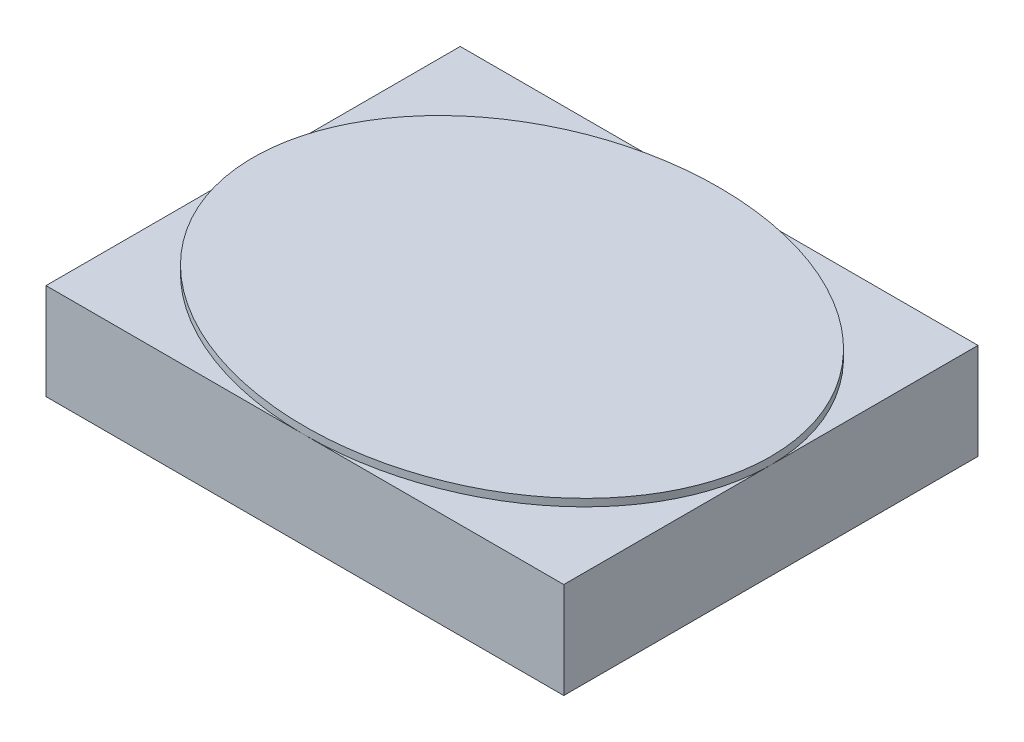
SolidWorks part; units mm, degrees
ref_plane "Front Plane" through (0, 0, 0) normal (0, 0, 1) x (1, 0, 0)
ref_plane "Top Plane" through (0, 0, 0) normal (0, 1, 0) x (1, 0, 0)
ref_plane "Right Plane" through (0, 0, 0) normal (1, 0, 0) x (0, 0, -1)
sketch "Sketch1" plane through (0, 0, 0) normal (0, 1, 0) x (1, 0, 0)
  line L1 (0, 0) -> (3.5, 0)
  line L2 (0, 0) -> (0, 2.8)
  line L3 (0, 2.8) -> (3.5, 2.8)
  line L4 (3.5, 0) -> (3.5, 2.8)
  dimension "D1" = 2.8
  dimension "D2" = 3.5
extrude "Boss-Extrude1" add sketch "Sketch1" along normal blind 0.65
sketch "Sketch3" plane through (0, 0.65, 0) normal (0, 1, 0) x (1, 0, 0)
  line L0 (1.75, 2.8) -> (1.75, 0) construction
  line L1 (3.5, 2.8) -> (0, 2.8) construction
  line L2 (0, 0) -> (3.5, 0) construction
  line L3 (3.5, 0) -> (3.5, 2.8) construction
  ellipse E0 centre (1.75, 1.4) end of major axis (3.5, 1.4) minor radius 1.4
extrude "Boss-Extrude2" add sketch "Sketch3" along normal blind 0.05
